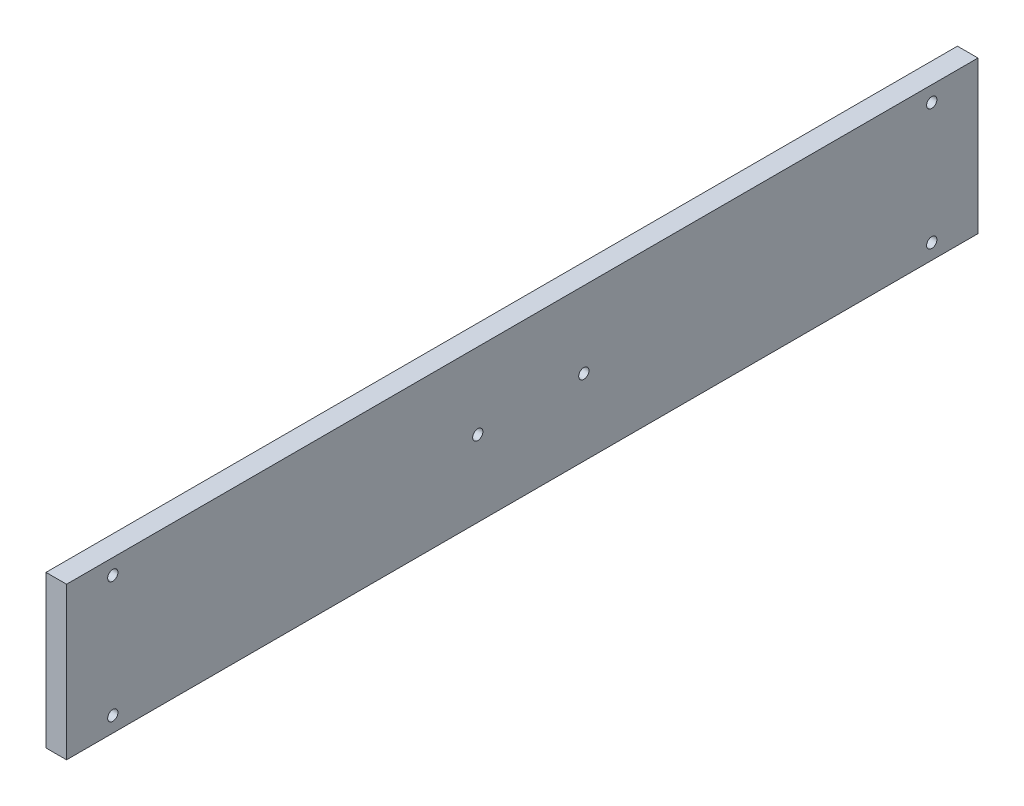
SolidWorks part; units mm, degrees
material "ABS"
ref_plane "Front Plane" through (0, 0, 0) normal (0, 0, 1) x (1, 0, 0)
ref_plane "Top Plane" through (0, 0, 0) normal (0, 1, 0) x (1, 0, 0)
ref_plane "Right Plane" through (0, 0, 0) normal (1, 0, 0) x (0, 0, -1)
sketch "Sketch1" plane through (0, 0, 0) normal (1, 0, 0) x (0, 0, -1)
  line L1 (-75, -37) -> (75, -37)
  line L2 (-75, -37) -> (-75, 37)
  line L3 (-75, 37) -> (75, 37)
  line L4 (75, -37) -> (75, 37)
  line L5 (-75, -37) -> (75, 37) construction
  line L6 (-75, 37) -> (75, -37) construction
  point P0 (0, 0)
  dimension "D1" = 74
  dimension "D2" = 150
extrude "Boss-Extrude1" add sketch "Sketch1" along normal blind 10
sketch "Sketch2" plane through (0, 0, -75) normal (0, 0, -1) x (-1, 0, 0)
  line L1 (0, 37) -> (-10, 37)
  line L2 (0, 37) -> (0, -37)
  line L3 (0, -37) -> (-10, -37)
  line L4 (-10, 37) -> (-10, -37)
extrude "Boss-Extrude2" add sketch "Sketch2" along normal offset from surface (283.4022 mm away) 10
sketch "Sketch3" plane through (0, 0, -358.4022) normal (0, 0, -1) x (-1, 0, 0)
  line L1 (0, 37) -> (-10, 37)
  line L2 (0, 37) -> (0, -37)
  line L3 (0, -37) -> (-10, -37)
  line L4 (-10, 37) -> (-10, -37)
extrude "Boss-Extrude3" add sketch "Sketch3" along normal blind 10
sketch "Sketch4" plane through (0, 0, 0) normal (-1, 0, 0) x (0, 0, 1)
  circle A0 centre (52.5, -29.5) radius 2.5
  circle A1 centre (52.5, 29.5) radius 2.5
  circle A2 centre (-345.9022, 29.5) radius 2.5
  circle A3 centre (-345.9022, -29.5) radius 2.5
extrude "Cut-Extrude1" cut sketch "Sketch4" against normal blind 10
sketch "Sketch5" plane through (10, 0, 0) normal (1, 0, 0) x (0, 0, -1)
  line L0 (-75, 37) -> (-75, -37) construction
  line L1 (368.4022, 37) -> (-75, 37) construction
  circle A0 centre (150.85, 0) radius 10
  dimension "D1" = 20
  dimension "D2" = 225.85
  dimension "D3" = 37
sketch "Sketch11" plane through (0, 0, 0) normal (-1, 0, 0) x (0, 0, 1)
  circle A0 centre (-125.052, 0) radius 2.5
  circle A1 centre (-176.648, 0) radius 2.5
  dimension "D1" = 5
  dimension "D2" = 5
extrude "Cut-Extrude2" cut sketch "Sketch11" against normal blind 10
